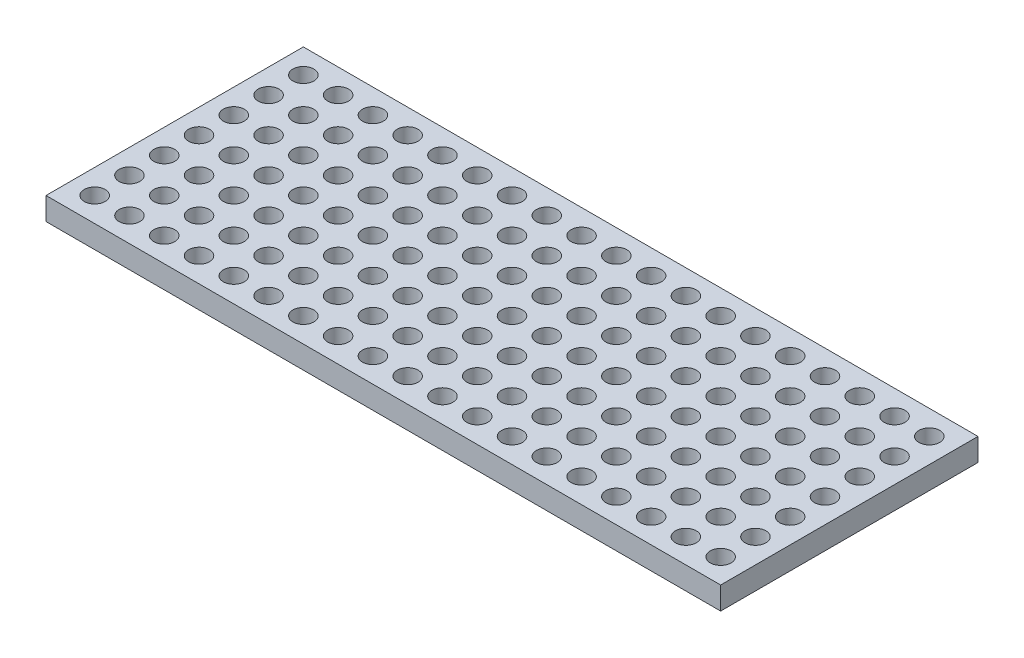
SolidWorks part; units mm, degrees
material "ABS"
ref_plane "Front Plane" through (0, 0, 0) normal (0, 0, 1) x (1, 0, 0)
ref_plane "Top Plane" through (0, 0, 0) normal (0, 1, 0) x (1, 0, 0)
ref_plane "Right Plane" through (0, 0, 0) normal (1, 0, 0) x (0, 0, -1)
sketch "Sketch1" plane through (0, 0, 0) normal (0, 1, 0) x (1, 0, 0)
  line L0 (-48.5, 18.5) -> (48.5, -18.5) construction
  line L1 (-48.5, 18.5) -> (48.5, 18.5)
  line L2 (-48.5, 18.5) -> (-48.5, -18.5)
  line L3 (-48.5, -18.5) -> (48.5, -18.5)
  line L4 (48.5, 18.5) -> (48.5, -18.5)
  circle A0 centre (-45, -15) radius 1.5025
  circle A1 centre (-40, -15) radius 1.5025
  circle A2 centre (-35, -15) radius 1.5025
  circle A3 centre (-30, -15) radius 1.5025
  circle A4 centre (-25, -15) radius 1.5025
  circle A5 centre (-20, -15) radius 1.5025
  circle A6 centre (-15, -15) radius 1.5025
  circle A7 centre (-10, -15) radius 1.5025
  circle A8 centre (-5, -15) radius 1.5025
  circle A9 centre (0, -15) radius 1.5025
  circle A10 centre (5, -15) radius 1.5025
  circle A11 centre (10, -15) radius 1.5025
  circle A12 centre (15, -15) radius 1.5025
  circle A13 centre (20, -15) radius 1.5025
  circle A14 centre (25, -15) radius 1.5025
  circle A15 centre (30, -15) radius 1.5025
  circle A16 centre (35, -15) radius 1.5025
  circle A17 centre (40, -15) radius 1.5025
  circle A18 centre (45, -15) radius 1.5025
  circle A19 centre (-40, -10) radius 1.5025
  circle A20 centre (-35, -10) radius 1.5025
  circle A21 centre (-30, -10) radius 1.5025
  circle A22 centre (-25, -10) radius 1.5025
  circle A23 centre (-20, -10) radius 1.5025
  circle A24 centre (-15, -10) radius 1.5025
  circle A25 centre (-10, -10) radius 1.5025
  circle A26 centre (-5, -10) radius 1.5025
  circle A27 centre (0, -10) radius 1.5025
  circle A28 centre (5, -10) radius 1.5025
  circle A29 centre (10, -10) radius 1.5025
  circle A30 centre (15, -10) radius 1.5025
  circle A31 centre (20, -10) radius 1.5025
  circle A32 centre (25, -10) radius 1.5025
  circle A33 centre (30, -10) radius 1.5025
  circle A34 centre (35, -10) radius 1.5025
  circle A35 centre (40, -10) radius 1.5025
  circle A36 centre (45, -10) radius 1.5025
  circle A37 centre (-40, -5) radius 1.5025
  circle A38 centre (-35, -5) radius 1.5025
  circle A39 centre (-30, -5) radius 1.5025
  circle A40 centre (-25, -5) radius 1.5025
  circle A41 centre (-20, -5) radius 1.5025
  circle A42 centre (-15, -5) radius 1.5025
  circle A43 centre (-10, -5) radius 1.5025
  circle A44 centre (-5, -5) radius 1.5025
  circle A45 centre (0, -5) radius 1.5025
  circle A46 centre (5, -5) radius 1.5025
  circle A47 centre (10, -5) radius 1.5025
  circle A48 centre (15, -5) radius 1.5025
  circle A49 centre (20, -5) radius 1.5025
  circle A50 centre (25, -5) radius 1.5025
  circle A51 centre (30, -5) radius 1.5025
  circle A52 centre (35, -5) radius 1.5025
  circle A53 centre (40, -5) radius 1.5025
  circle A54 centre (45, -5) radius 1.5025
  circle A55 centre (-40, 0) radius 1.5025
  circle A56 centre (-35, 0) radius 1.5025
  circle A57 centre (-30, 0) radius 1.5025
  circle A58 centre (-25, 0) radius 1.5025
  circle A59 centre (-20, 0) radius 1.5025
  circle A60 centre (-15, 0) radius 1.5025
  circle A61 centre (-10, 0) radius 1.5025
  circle A62 centre (-5, 0) radius 1.5025
  circle A63 centre (0, 0) radius 1.5025
  circle A64 centre (5, 0) radius 1.5025
  circle A65 centre (10, 0) radius 1.5025
  circle A66 centre (15, 0) radius 1.5025
  circle A67 centre (20, 0) radius 1.5025
  circle A68 centre (25, 0) radius 1.5025
  circle A69 centre (30, 0) radius 1.5025
  circle A70 centre (35, 0) radius 1.5025
  circle A71 centre (40, 0) radius 1.5025
  circle A72 centre (45, 0) radius 1.5025
  circle A73 centre (-40, 5) radius 1.5025
  circle A74 centre (-35, 5) radius 1.5025
  circle A75 centre (-30, 5) radius 1.5025
  circle A76 centre (-25, 5) radius 1.5025
  circle A77 centre (-20, 5) radius 1.5025
  circle A78 centre (-15, 5) radius 1.5025
  circle A79 centre (-10, 5) radius 1.5025
  circle A80 centre (-5, 5) radius 1.5025
  circle A81 centre (0, 5) radius 1.5025
  circle A82 centre (5, 5) radius 1.5025
  circle A83 centre (10, 5) radius 1.5025
  circle A84 centre (15, 5) radius 1.5025
  circle A85 centre (20, 5) radius 1.5025
  circle A86 centre (25, 5) radius 1.5025
  circle A87 centre (30, 5) radius 1.5025
  circle A88 centre (35, 5) radius 1.5025
  circle A89 centre (40, 5) radius 1.5025
  circle A90 centre (45, 5) radius 1.5025
  circle A91 centre (-40, 10) radius 1.5025
  circle A92 centre (-35, 10) radius 1.5025
  circle A93 centre (-30, 10) radius 1.5025
  circle A94 centre (-25, 10) radius 1.5025
  circle A95 centre (-20, 10) radius 1.5025
  circle A96 centre (-15, 10) radius 1.5025
  circle A97 centre (-10, 10) radius 1.5025
  circle A98 centre (-5, 10) radius 1.5025
  circle A99 centre (0, 10) radius 1.5025
  circle A100 centre (5, 10) radius 1.5025
  circle A101 centre (10, 10) radius 1.5025
  circle A102 centre (15, 10) radius 1.5025
  circle A103 centre (20, 10) radius 1.5025
  circle A104 centre (25, 10) radius 1.5025
  circle A105 centre (30, 10) radius 1.5025
  circle A106 centre (35, 10) radius 1.5025
  circle A107 centre (40, 10) radius 1.5025
  circle A108 centre (45, 10) radius 1.5025
  circle A109 centre (-40, 15) radius 1.5025
  circle A110 centre (-35, 15) radius 1.5025
  circle A111 centre (-30, 15) radius 1.5025
  circle A112 centre (-25, 15) radius 1.5025
  circle A113 centre (-20, 15) radius 1.5025
  circle A114 centre (-15, 15) radius 1.5025
  circle A115 centre (-10, 15) radius 1.5025
  circle A116 centre (-5, 15) radius 1.5025
  circle A117 centre (0, 15) radius 1.5025
  circle A118 centre (5, 15) radius 1.5025
  circle A119 centre (10, 15) radius 1.5025
  circle A120 centre (15, 15) radius 1.5025
  circle A121 centre (20, 15) radius 1.5025
  circle A122 centre (25, 15) radius 1.5025
  circle A123 centre (30, 15) radius 1.5025
  circle A124 centre (35, 15) radius 1.5025
  circle A125 centre (40, 15) radius 1.5025
  circle A126 centre (45, 15) radius 1.5025
  circle A127 centre (-45, -10) radius 1.5025
  circle A128 centre (-45, -5) radius 1.5025
  circle A129 centre (-45, 0) radius 1.5025
  circle A130 centre (-45, 5) radius 1.5025
  circle A131 centre (-45, 10) radius 1.5025
  circle A132 centre (-45, 15) radius 1.5025
  dimension "D3" = 3.005
  dimension "D4" = 3.5
  dimension "D5" = 3.5
  dimension "D9" = 3.5
  dimension "D10" = 3.5
  dimension "D11" = 3.5
  dimension "D1" = 97
  dimension "D2" = 37
  dimension "D6" = 19
  dimension "D7" = 7
  dimension "D8" = 3.5
extrude "Boss-Extrude1" add sketch "Sketch1" along normal blind 3.25
